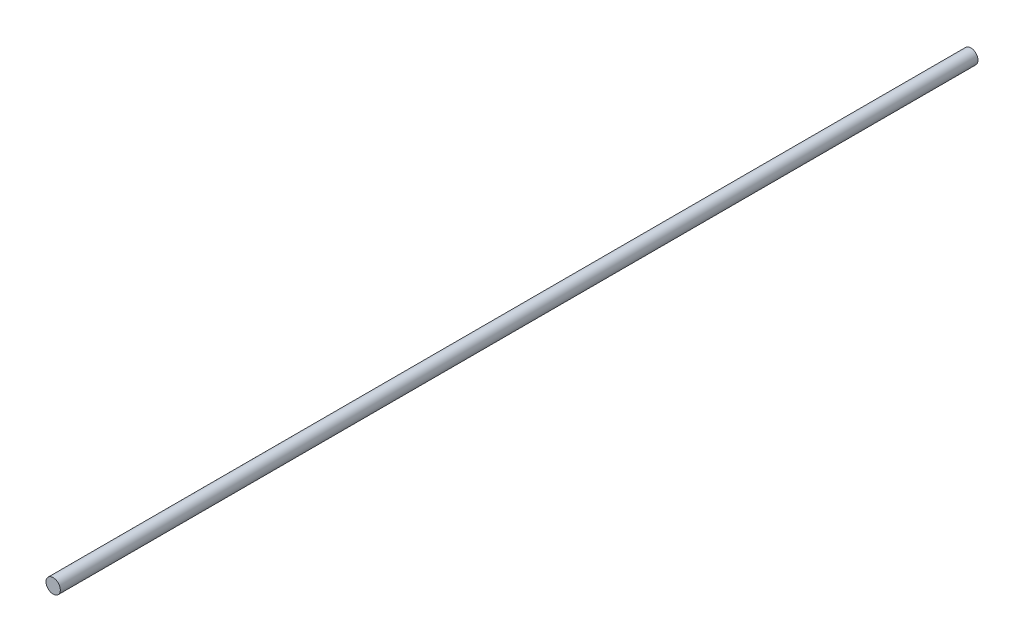
SolidWorks part; units mm, degrees
material "6061 Alloy"
ref_plane "Front Plane" through (0, 0, 0) normal (0, 0, 1) x (1, 0, 0)
ref_plane "Top Plane" through (0, 0, 0) normal (0, 1, 0) x (1, 0, 0)
ref_plane "Right Plane" through (0, 0, 0) normal (1, 0, 0) x (0, 0, -1)
sketch "Sketch1" plane through (0, 0, 0) normal (0, 0, 1) x (1, 0, 0)
  circle A0 centre (0, 0) radius 3.175
  dimension "D1" = 6.35
extrude "Boss-Extrude1" add sketch "Sketch1" along normal blind 406.4
